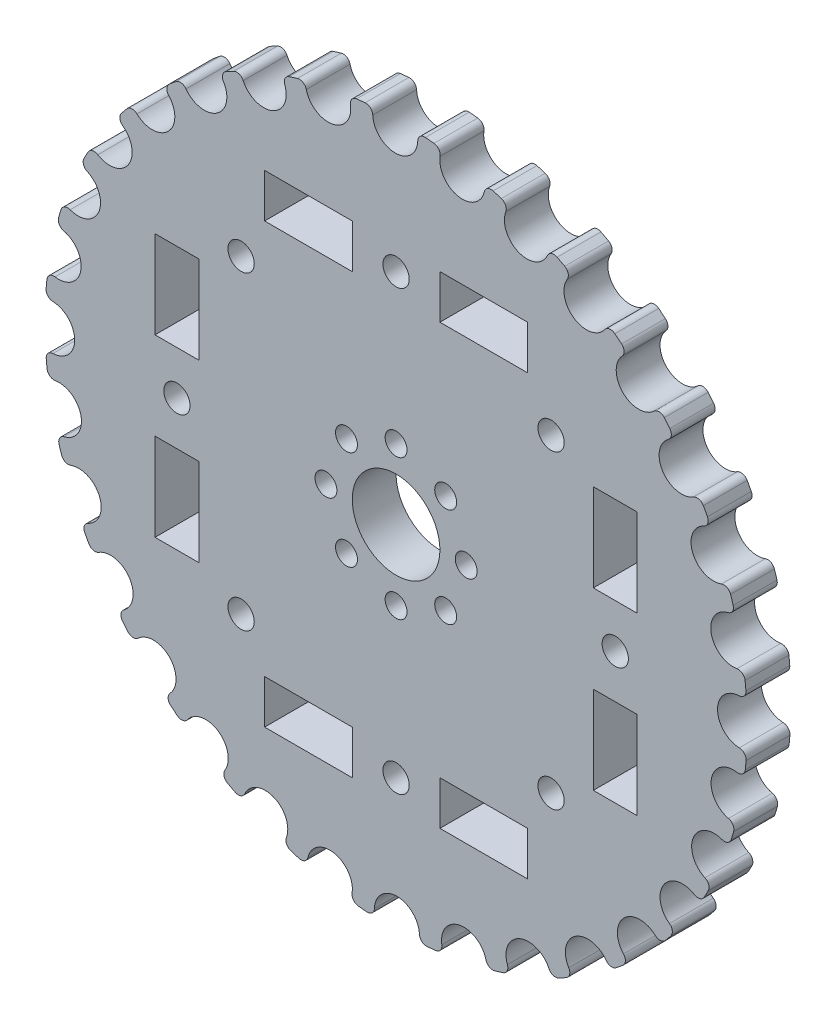
SolidWorks part; units mm, degrees
material "PMMA"
ref_plane "Front Plane" through (0, 0, 0) normal (0, 0, 1) x (1, 0, 0)
ref_plane "Top Plane" through (0, 0, 0) normal (0, 1, 0) x (1, 0, 0)
ref_plane "Right Plane" through (0, 0, 0) normal (1, 0, 0) x (0, 0, -1)
sketch "Schizzo1" plane through (0, 0, 0) normal (0, 0, 1) x (1, 0, 0)
  circle A0 centre (0, 0) radius 40.7437 construction
  circle A1 centre (0, 0) radius 40.0627
  circle A3 centre (0, 0) radius 36.6117 construction
  dimension "D1" = 81.4873
  dimension "D2" = 80.1253
  dimension "D4" = 73.2233
  dimension "D3" = 0.681
extrude "Estrusione-Estrusione1" add sketch "Schizzo1" along normal blind 5
sketch "Schizzo2" plane through (0, 0, 0) normal (0, 0, 1) x (1, 0, 0)
  line L0 (0.0019, 0) -> (-0.0935, 39.2349) construction
  line L1 (0.0019, 0) -> (7.5627, 38.4996) construction
  circle A0 centre (0, 0) radius 40.7437 construction
  circle A1 centre (0, 0) radius 36.665 construction
  circle A2 centre (-0.0935, 39.2349) radius 2.57
  circle A3 centre (7.5627, 38.4996) radius 2.57
  circle A4 centre (14.9283, 36.2848) radius 2.57
  circle A5 centre (21.7203, 32.6756) radius 2.57
  circle A6 centre (27.6777, 27.8107) radius 2.57
  circle A7 centre (32.5715, 21.8771) radius 2.57
  circle A8 centre (36.2137, 15.1027) radius 2.57
  circle A9 centre (38.4643, 7.7479) radius 2.57
  circle A10 centre (39.2368, 0.0954) radius 2.57
  circle A11 centre (38.5015, -7.5608) radius 2.57
  circle A12 centre (36.2867, -14.9264) radius 2.57
  circle A13 centre (32.6775, -21.7184) radius 2.57
  circle A14 centre (27.8126, -27.6758) radius 2.57
  circle A15 centre (21.8789, -32.5696) radius 2.57
  circle A16 centre (15.1046, -36.2118) radius 2.57
  circle A17 centre (7.7498, -38.4624) radius 2.57
  circle A18 centre (0.0973, -39.2349) radius 2.57
  circle A19 centre (-7.5589, -38.4996) radius 2.57
  circle A20 centre (-14.9245, -36.2848) radius 2.57
  circle A21 centre (-21.7165, -32.6756) radius 2.57
  circle A22 centre (-27.6739, -27.8107) radius 2.57
  circle A23 centre (-32.5677, -21.8771) radius 2.57
  circle A24 centre (-36.2099, -15.1027) radius 2.57
  circle A25 centre (-38.4605, -7.7479) radius 2.57
  circle A26 centre (-39.233, -0.0954) radius 2.57
  circle A27 centre (-38.4977, 7.5608) radius 2.57
  circle A28 centre (-36.2829, 14.9264) radius 2.57
  circle A29 centre (-32.6737, 21.7184) radius 2.57
  circle A30 centre (-27.8088, 27.6758) radius 2.57
  circle A31 centre (-21.8752, 32.5696) radius 2.57
  circle A32 centre (-15.1008, 36.2118) radius 2.57
  circle A33 centre (-7.746, 38.4624) radius 2.57
  point P70 (0.0019, 0)
  dimension "D1" = 81.4873
  dimension "D7" = 5.14
  dimension "D2" = 73.33
  dimension "D6" = 7.6914
  dimension "D5" = 11.25
  dimension "D3" = 32
extrude "Taglio-Estrusione1" cut sketch "Schizzo2" along direction (0, 0, 1) on the side of the normal through all
fillet "Raccordo1" radius 0.8 64 edges at (-5.4856, 39.6853, 2.5) (-10.3036, 38.715, 2.5) (-13.1227, 37.8525, 2.5) (-17.6585, 35.961, 2.5) (-20.2554, 34.5649, 2.5) (-24.3349, 31.825, 2.5) (-26.6098, 29.9489, 2.5) (-30.0762, 26.4658, 2.5) (-31.9414, 24.1819, 2.5) (-34.6616, 20.0895, 2.5) (-36.0455, 17.4854, 2.5) (-37.915, 12.9411, 2.5) (-38.7642, 10.1169, 2.5) (-39.7112, 5.2953, 2.5) (-39.9931, 2.3596, 2.5) (-39.9812, -2.5541, 2.5) (-39.6849, -5.4883, 2.5) (-38.7146, -10.3053, 2.5) (-37.8516, -13.1253, 2.5) (-35.96, -17.6605, 2.5) (-34.5635, -20.2579, 2.5) (-31.8234, -24.3369, 2.5) (-29.9471, -26.6118, 2.5) (-26.4638, -30.078, 2.5) (-24.1799, -31.9429, 2.5) (-20.0871, -34.663, 2.5) (-17.4834, -36.0464, 2.5) (-12.9384, -37.9159, 2.5) (-10.1152, -38.7647, 2.5) (-5.2926, -39.7115, 2.5) (-2.3583, -39.9932, 2.5) (2.5566, -39.981, 2.5) (5.4891, -39.6848, 2.5) (10.3075, -38.714, 2.5) (13.1256, -37.8515, 2.5) (17.6621, -35.9592, 2.5) (20.2576, -34.5637, 2.5) (24.338, -31.8226, 2.5) (26.6112, -29.9477, 2.5) (30.0785, -26.4632, 2.5) (31.9421, -24.181, 2.5) (34.6632, -20.0868, 2.5) (36.0457, -17.4851, 2.5) (37.9158, -12.9387, 2.5) (38.7641, -10.1173, 2.5) (39.7114, -5.2934, 2.5) (39.993, -2.3608, 2.5) (39.9811, 2.5553, 2.5) (39.6852, 5.4865, 2.5) (38.7145, 10.3057, 2.5) (37.8524, 13.1229, 2.5) (35.9602, 17.6601, 2.5) (34.5651, 20.2552, 2.5) (31.8241, 24.336, 2.5) (29.9495, 26.6091, 2.5) (26.4652, 30.0767, 2.5) (24.1829, 31.9406, 2.5) (20.0893, 34.6618, 2.5) (17.487, 36.0447, 2.5) (12.9414, 37.9149, 2.5) (10.1191, 38.7637, 2.5) (5.2961, 39.7111, 2.5) (2.3621, 39.993, 2.5) (-2.5528, 39.9812, 2.5)
sketch "Schizzo3" plane through (0, 0, 0) normal (0, 0, 1) x (1, 0, 0)
  circle A0 centre (0, 0) radius 5
  dimension "D1" = 10
extrude "Taglio-Estrusione2" cut sketch "Schizzo3" along direction (0, 0, 1) on the side of the normal through all
sketch "Schizzo4" plane through (0, 0, 0) normal (0, 0, 1) x (1, 0, 0)
  line L0 (0, 0) -> (0, 8) construction
  line L1 (0, 0) -> (0, 25) construction
  line L2 (0, -2.6008) -> (0, 40.6044) construction
  line L3 (0.0469, 0) -> (-50.6046, 0) construction
  line L4 (0, 0) -> (5.6569, 5.6569) construction
  line L5 (-25, -7.071) -> (-25, 7.0711) construction
  line L6 (-22.5, 5) -> (-27.5, 5)
  line L7 (-22.5, 5) -> (-22.5, 15)
  line L8 (-22.5, 15) -> (-27.5, 15)
  line L9 (-27.5, 5) -> (-27.5, 15)
  line L10 (-22.5, -5) -> (-27.5, -5)
  line L11 (-22.5, -5) -> (-22.5, -15)
  line L12 (-22.5, -15) -> (-27.5, -15)
  line L13 (-27.5, -5) -> (-27.5, -15)
  line L14 (5, 27.5) -> (15, 27.5)
  line L15 (15, 22.5) -> (15, 27.5)
  line L16 (5, 22.5) -> (15, 22.5)
  line L17 (5, 22.5) -> (5, 27.5)
  line L18 (-5, 27.5) -> (-15, 27.5)
  line L19 (-15, 22.5) -> (-15, 27.5)
  line L20 (-5, 22.5) -> (-15, 22.5)
  line L21 (-5, 22.5) -> (-5, 27.5)
  line L22 (27.5, -5) -> (27.5, -15)
  line L23 (22.5, -15) -> (27.5, -15)
  line L24 (22.5, -5) -> (22.5, -15)
  line L25 (22.5, -5) -> (27.5, -5)
  line L26 (27.5, 5) -> (27.5, 15)
  line L27 (22.5, 15) -> (27.5, 15)
  line L28 (22.5, 5) -> (22.5, 15)
  line L29 (22.5, 5) -> (27.5, 5)
  line L30 (-5, -27.5) -> (-15, -27.5)
  line L31 (-15, -22.5) -> (-15, -27.5)
  line L32 (-5, -22.5) -> (-15, -22.5)
  line L33 (-5, -22.5) -> (-5, -27.5)
  line L34 (5, -27.5) -> (15, -27.5)
  line L35 (15, -22.5) -> (15, -27.5)
  line L36 (5, -22.5) -> (15, -22.5)
  line L37 (5, -22.5) -> (5, -27.5)
  line L38 (0, 0) -> (-22.5, -5) construction
  circle A0 centre (0, 8) radius 1.25
  circle A1 centre (5.6569, 5.6569) radius 1.25
  circle A2 centre (8, 0) radius 1.25
  circle A3 centre (5.6569, -5.6569) radius 1.25
  circle A4 centre (0, -8) radius 1.25
  circle A5 centre (-5.6569, -5.6569) radius 1.25
  circle A6 centre (-8, 0) radius 1.25
  circle A7 centre (-5.6569, 5.6569) radius 1.25
  circle A8 centre (0, 25) radius 1.5
  circle A9 centre (17.6777, 17.6777) radius 1.5
  circle A10 centre (25, 0) radius 1.5
  circle A11 centre (17.6777, -17.6777) radius 1.5
  circle A12 centre (0, -25) radius 1.5
  circle A13 centre (-17.6777, -17.6777) radius 1.5
  circle A14 centre (-25, 0) radius 1.5
  circle A15 centre (-17.6777, 17.6777) radius 1.5
  point P0 (0, 0)
  point P47 (-25, 5)
  point P54 (0, 0)
  dimension "D1" = 2.5
  dimension "D5" = 3
  dimension "D8" = 25
  dimension "D4" = 8
  dimension "D6" = 45
  dimension "D9" = 5
  dimension "D10" = 5
  dimension "D11" = 10
  dimension "D3" = 8
  dimension "D7" = 8
  dimension "D12" = 4
extrude "Taglio-Estrusione3" cut sketch "Schizzo4" along direction (0, 0, 1) on the side of the normal through all
equation "\"PD\"= ( \"Pitch\" * \"N\" ) / 3.141593'Pitch Diameter"
equation "\"D1@Schizzo1\"=\"PD\""
equation "\"Pitch\"= 8"
equation "\"N\"= 32'Number of Teeth"
equation "\"OD\"= \"PD\" - 2 * \"U\"'Outer Diameter"
equation "\"h_t\"= 3.451mm'Height of the tooth"
equation "\"D2@Schizzo1\"=\"OD\""
equation "\"D3@Schizzo1\"=\"h_t\""
equation "\"U\"= 0.681'distance between the tensile cord and the bottom of the belt tooth"
equation "\"Thickness5\"=5"
equation "\"D1@Estrusione-Estrusione1\"=\"Thickness5\""
equation "\"D1@Schizzo2\"=\"PD\""
equation "\"D_t\"=5.14"
equation "\"D7@Schizzo2\"=\"D_t\""
equation "\"R\"=0.15"
equation "\"D1@Raccordo1\"=\"R_t\""
equation "\"R_t\"=0.8"
equation "\"ID\"= \"OD\" - 2 * \"h_t\""
equation "\"D4@Schizzo1\"=\"ID\""
equation "\"D9@Schizzo4\"=\"Thickness5\""
